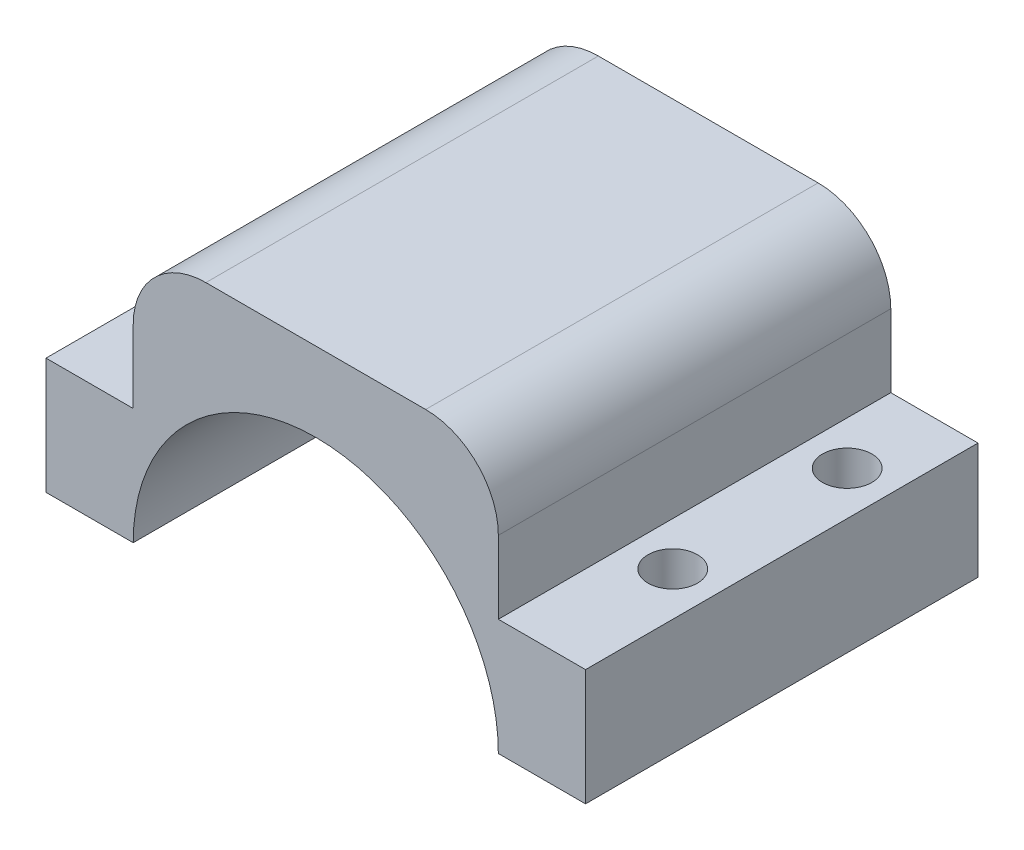
SolidWorks part; units mm, degrees
ref_plane "Plan de face" through (0, 0, 0) normal (0, 0, 1) x (1, 0, 0)
ref_plane "Plan de dessus" through (0, 0, 0) normal (0, 1, 0) x (1, 0, 0)
ref_plane "Plan de droite" through (0, 0, 0) normal (1, 0, 0) x (0, 0, -1)
sketch "Esquisse1" plane through (0, 0, 0) normal (0, 0, 1) x (1, 0, 0)
  line L0 (0, 0) -> (-84.6745, 0) construction
  line L1 (0, 0) -> (94.0931, 0) construction
  line L2 (-12.5601, 0) -> (-18.5601, 0)
  line L3 (0, 0) -> (0, 12.5601) construction
  line L4 (-18.5601, 0) -> (-18.5601, 18)
  line L5 (-18.5601, 18) -> (18.5601, 18)
  line L6 (18.5601, 0) -> (18.5601, 18)
  line L7 (12.5601, 0) -> (18.5601, 0)
  line L8 (0, 12.5601) -> (0, 18) construction
  arc A0 (-12.5601, 0) -> (12.5601, 0) centre (0, 0) cw
  point P11 (0, 18)
  dimension "D1" = 6
  dimension "D2" = 18
extrude "Boss.-Extru.1" add sketch "Esquisse1" along normal blind 27
sketch "Esquisse5" plane through (0, 18, 0) normal (0, 1, 0) x (1, 0, 0)
  line L0 (18.5601, -13.5) -> (-18.5601, -13.5) construction
  line L1 (18.5601, -27) -> (18.5601, 0) construction
  line L2 (-18.5601, -27) -> (-18.5601, 0) construction
  line L3 (0, 0) -> (0, -27) construction
  line L4 (18.5601, 0) -> (-18.5601, 0) construction
  line L5 (18.5601, -27) -> (-18.5601, -27) construction
  line L6 (15.5601, 0) -> (15.5601, -27) construction
  line L7 (18.5601, -6) -> (-18.5601, -6) construction
  line L8 (18.5601, 0) -> (18.5601, -27) construction
  line L9 (18.5601, -27) -> (-18.5601, -27) construction
  line L10 (-18.5601, -27) -> (-18.5601, 0) construction
  line L11 (-18.5601, 0) -> (18.5601, 0) construction
  circle A0 centre (15.5601, -6) radius 1.7
  circle A1 centre (15.5601, -18) radius 1.7
  circle A2 centre (-15.5601, -6) radius 1.7
  circle A3 centre (-15.5601, -18) radius 1.7
  dimension "D3" = 2
  dimension "D1" = 3
  dimension "D2" = 6
extrude "Enlèv. mat.-Extru.1" cut sketch "Esquisse5" against normal blind 18
sketch "Esquisse6" plane through (0, 18, 0) normal (0, 1, 0) x (1, 0, 0)
  line L0 (18.5601, -27) -> (-18.5601, -27) construction
  line L1 (18.5601, 0) -> (12.5601, 0)
  line L2 (18.5601, 0) -> (18.5601, -27)
  line L3 (18.5601, -27) -> (12.5601, -27)
  line L4 (12.5601, 0) -> (12.5601, -27)
  line L5 (0, 0) -> (0, -27) construction
  line L6 (18.5601, 0) -> (-18.5601, 0) construction
  line L7 (-12.5601, 0) -> (-12.5601, -27)
  line L8 (-18.5601, -27) -> (-12.5601, -27)
  line L9 (-18.5601, 0) -> (-18.5601, -27)
  line L10 (-18.5601, 0) -> (-12.5601, 0)
  dimension "D1" = 6
extrude "Enlèv. mat.-Extru.2" cut sketch "Esquisse6" against normal blind 10
fillet "Congé1" radius 5 2 edges at (-12.5601, 18, 13.5) (12.5601, 18, 13.5)
